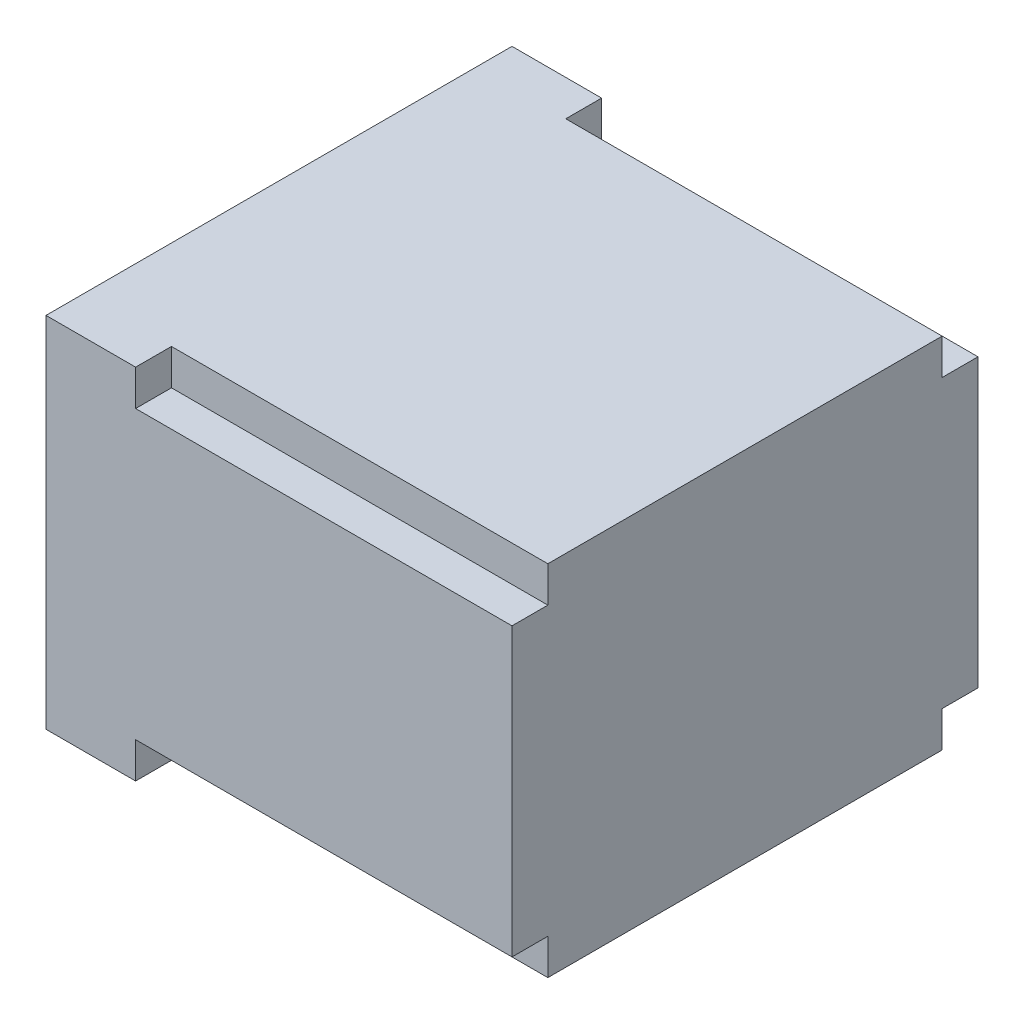
SolidWorks part; units mm, degrees
ref_plane "Front Plane" through (0, 0, 0) normal (0, 0, 1) x (1, 0, 0)
ref_plane "Top Plane" through (0, 0, 0) normal (0, 1, 0) x (1, 0, 0)
ref_plane "Right Plane" through (0, 0, 0) normal (1, 0, 0) x (0, 0, -1)
sketch "Sketch2" plane through (0, 0, 0) normal (0, 1, 0) x (1, 0, 0)
  line L1 (0, 0) -> (130, 0)
  line L2 (0, 0) -> (0, 130)
  line L3 (0, 130) -> (130, 130)
  line L4 (130, 0) -> (130, 130)
  dimension "D1" = 130
  dimension "D2" = 130
extrude "Boss-Extrude1" add sketch "Sketch2" along normal blind 100
sketch "Sketch3" plane through (0, 0, 0) normal (-1, 0, 0) x (0, 0, 1)
  line L0 (-130, 100) -> (0, 100) construction
  line L1 (-117, 13) -> (-13, 13)
  line L2 (-117, 13) -> (-117, 87)
  line L3 (-117, 87) -> (-13, 87)
  line L4 (-13, 13) -> (-13, 87)
  line L5 (0, 100) -> (0, 0) construction
  line L6 (-130, 0) -> (0, 0) construction
  line L7 (-130, 100) -> (-130, 0) construction
  dimension "D1" = 13
  dimension "D2" = 13
  dimension "D3" = 13
  dimension "D4" = 13
extrude "Cut-Extrude1" cut sketch "Sketch3" against normal blind 127
sketch "Sketch4" plane through (130, 0, 0) normal (1, 0, 0) x (0, 0, -1)
  line L1 (0, 100) -> (10, 100)
  line L2 (0, 100) -> (0, 90)
  line L3 (0, 90) -> (10, 90)
  line L4 (10, 100) -> (10, 90)
  line L5 (130, 100) -> (120, 100)
  line L6 (130, 100) -> (130, 90)
  line L7 (130, 90) -> (120, 90)
  line L8 (120, 100) -> (120, 90)
  line L9 (0, 0) -> (10, 0)
  line L10 (0, 0) -> (0, 10)
  line L11 (0, 10) -> (10, 10)
  line L12 (10, 0) -> (10, 10)
  line L13 (130, 0) -> (120, 0)
  line L14 (130, 0) -> (130, 10)
  line L15 (130, 10) -> (120, 10)
  line L16 (120, 0) -> (120, 10)
  dimension "D1" = 10
  dimension "D2" = 10
  dimension "D3" = 10
  dimension "D4" = 10
  dimension "D5" = 10
  dimension "D6" = 10
  dimension "D7" = 10
  dimension "D8" = 10
extrude "Cut-Extrude3" cut sketch "Sketch4" against normal blind 105
sketch "Sketch5" plane through (0, 0, 0) normal (-1, 0, 0) x (0, 0, 1)
  line L0 (-130, 100) -> (0, 100) construction
  line L1 (-117, 87) -> (-13, 87)
  line L2 (-117, 87) -> (-117, 97)
  line L3 (-117, 97) -> (-13, 97)
  line L4 (-13, 87) -> (-13, 97)
  line L5 (-117, 13) -> (-13, 13)
  line L6 (-117, 13) -> (-117, 3)
  line L7 (-117, 3) -> (-13, 3)
  line L8 (-13, 13) -> (-13, 3)
  line L9 (-130, 0) -> (0, 0) construction
  line L10 (0, 100) -> (0, 0) construction
  dimension "D1" = 3
  dimension "D2" = 3
  dimension "D3" = 13
  dimension "D4" = 13
extrude "Cut-Extrude4" cut sketch "Sketch5" against normal blind 127
sketch "Sketch6" plane through (0, 0, 0) normal (-1, 0, 0) x (0, 0, 1)
  line L0 (-117, 97) -> (-117, 3) construction
  line L1 (-117, 87) -> (-127, 87)
  line L2 (-117, 87) -> (-117, 13)
  line L3 (-117, 13) -> (-127, 13)
  line L4 (-127, 87) -> (-127, 13)
  line L5 (-13, 3) -> (-13, 97) construction
  line L6 (-13, 87) -> (-3, 87)
  line L7 (-13, 87) -> (-13, 13)
  line L8 (-13, 13) -> (-3, 13)
  line L9 (-3, 87) -> (-3, 13)
  line L10 (-130, 100) -> (-130, 0) construction
  line L11 (0, 100) -> (0, 0) construction
  line L12 (-130, 100) -> (0, 100) construction
  line L13 (-130, 0) -> (0, 0) construction
  dimension "D1" = 3
  dimension "D2" = 3
  dimension "D3" = 13
  dimension "D4" = 13
  dimension "D5" = 13
  dimension "D6" = 13
extrude "Cut-Extrude5" cut sketch "Sketch6" against normal blind 127
sketch "Sketch7" plane through (0, 0, 0) normal (-1, 0, 0) x (0, 0, 1)
  line L0 (0, 100) -> (0, 0) construction
  line L1 (-130, 0) -> (0, 0) construction
  line L2 (-130, 100) -> (-130, 0) construction
  line L3 (-130, 100) -> (0, 100) construction
  circle A0 centre (-124, 94) radius 1.75
  circle A1 centre (-6, 94) radius 1.75
  circle A2 centre (-124, 6) radius 1.75
  circle A3 centre (-6, 6) radius 1.75
  dimension "D3" = 3.5
  dimension "D6" = 3.5
  dimension "D9" = 3.5
  dimension "D12" = 3.5
  dimension "D1" = 6
  dimension "D2" = 6
  dimension "D4" = 6
  dimension "D5" = 6
  dimension "D7" = 6
  dimension "D8" = 6
  dimension "D10" = 6
  dimension "D11" = 6
extrude "Cut-Extrude6" cut sketch "Sketch7" against normal blind 20
sketch "Sketch8" plane through (0, 0, 0) normal (-1, 0, 0) x (0, 0, 1)
  line L1 (-117, 87) -> (-120, 87)
  line L2 (-117, 87) -> (-117, 90)
  line L3 (-117, 90) -> (-120, 90)
  line L4 (-120, 87) -> (-120, 90)
  line L5 (-13, 87) -> (-10, 87)
  line L6 (-13, 87) -> (-13, 90)
  line L7 (-13, 90) -> (-10, 90)
  line L8 (-10, 87) -> (-10, 90)
  line L9 (-117, 13) -> (-120, 13)
  line L10 (-117, 13) -> (-117, 10)
  line L11 (-117, 10) -> (-120, 10)
  line L12 (-120, 13) -> (-120, 10)
  line L13 (-13, 13) -> (-10, 13)
  line L14 (-13, 13) -> (-13, 10)
  line L15 (-13, 10) -> (-10, 10)
  line L16 (-10, 13) -> (-10, 10)
  dimension "D1" = 3
  dimension "D2" = 3
  dimension "D3" = 3
  dimension "D4" = 3
  dimension "D5" = 3
  dimension "D6" = 3
  dimension "D7" = 3
  dimension "D8" = 3
extrude "Cut-Extrude7" cut sketch "Sketch8" against normal blind 5
sketch "Sketch9" plane through (0, 3, 0) normal (0, 1, 0) x (1, 0, 0)
  line L1 (0, 117) -> (85, 117)
  line L2 (0, 117) -> (0, 57)
  line L3 (0, 57) -> (85, 57)
  line L4 (85, 117) -> (85, 57)
  dimension "D1" = 60
  dimension "D2" = 85
extrude "Boss-Extrude2" add sketch "Sketch9" along normal blind 15
sketch "Sketch11" plane through (0, 13, 0) normal (0, 1, 0) x (1, 0, 0)
  line L0 (0, 127) -> (0, 120) construction
  line L5 (85, 117) -> (0, 117)
  line L6 (85, 117) -> (85, 123)
  line L7 (85, 123) -> (0, 123)
  line L8 (0, 117) -> (0, 123)
  dimension "D1" = 6
extrude "Boss-Extrude5" add sketch "Sketch11" along normal blind 5
sketch "Sketch12" plane through (0, 18, 0) normal (0, 1, 0) x (1, 0, 0)
  line L0 (85, 57) -> (85, 123) construction
  line L1 (0, 123) -> (85, 123)
  line L2 (0, 123) -> (0, 120)
  line L3 (0, 120) -> (85, 120)
  line L4 (85, 123) -> (85, 120)
  dimension "D1" = 3
extrude "Cut-Extrude9" cut sketch "Sketch12" against normal blind 4
sketch "Sketch13" plane through (0, 18, 0) normal (0, 1, 0) x (1, 0, 0)
  line L0 (85, 57) -> (85, 120) construction
  line L1 (82, 117) -> (0, 117)
  line L2 (82, 117) -> (82, 60)
  line L3 (82, 60) -> (0, 60)
  line L4 (0, 117) -> (0, 60)
  line L5 (0, 57) -> (85, 57) construction
  line L6 (0, 120) -> (85, 120) construction
  line L7 (0, 120) -> (0, 57) construction
  dimension "D1" = 3
  dimension "D2" = 3
  dimension "D3" = 3
  dimension "D4" = 0
extrude "Cut-Extrude10" cut sketch "Sketch13" against normal blind 15
sketch "Sketch15" plane through (5, 0, 0) normal (-1, 0, 0) x (0, 0, 1)
  line L1 (-120, 13) -> (-117, 13)
  line L2 (-120, 13) -> (-120, 10)
  line L3 (-120, 10) -> (-117, 10)
  line L4 (-117, 13) -> (-117, 10)
extrude "Boss-Extrude7" add sketch "Sketch15" along normal blind 5
sketch "Sketch16" plane through (0, 0, -60) normal (0, 0, -1) x (-1, 0, 0)
  line L0 (0, 3) -> (0, 18) construction
  line L1 (-82, 18) -> (0, 18)
  line L2 (-82, 18) -> (-82, 16)
  line L3 (-82, 16) -> (0, 16)
  line L4 (0, 18) -> (0, 16)
  line L5 (-82, 3) -> (-82, 18) construction
  line L6 (-82, 13) -> (0, 13)
  line L7 (-82, 13) -> (-82, 11)
  line L8 (-82, 11) -> (0, 11)
  line L9 (0, 13) -> (0, 11)
  dimension "D1" = 2
  dimension "D2" = 2
  dimension "D3" = 3
extrude "Boss-Extrude8" add sketch "Sketch16" along normal blind 57
sketch "Sketch17" plane through (0, 18, 0) normal (0, 1, 0) x (1, 0, 0)
  line L0 (0, 120) -> (0, 57) construction
  line L1 (0, 112) -> (77, 112)
  line L2 (0, 112) -> (0, 65)
  line L3 (0, 65) -> (77, 65)
  line L4 (77, 112) -> (77, 65)
  line L5 (0, 57) -> (85, 57) construction
  line L6 (85, 57) -> (85, 120) construction
  line L7 (0, 120) -> (85, 120) construction
  dimension "D1" = 8
  dimension "D2" = 8
  dimension "D3" = 8
extrude "Cut-Extrude11" cut sketch "Sketch17" against normal blind 10
sketch "Sketch19" plane through (0, 0, -117) normal (0, 0, 1) x (1, 0, 0)
  line L1 (0, 11) -> (7, 11)
  line L2 (0, 11) -> (0, 9)
  line L3 (0, 9) -> (7, 9)
  line L4 (7, 11) -> (7, 9)
  line L5 (0, 13) -> (7, 13)
  line L6 (0, 13) -> (0, 14)
  line L7 (0, 14) -> (7, 14)
  line L8 (7, 13) -> (7, 14)
  dimension "D1" = 2
  dimension "D2" = 7
  dimension "D3" = 7
  dimension "D4" = 1
extrude "Boss-Extrude9" add sketch "Sketch19" along normal blind 1
sketch "Sketch21" plane through (0, 0, 0) normal (-1, 0, 0) x (0, 0, 1)
  line L0 (-130, 0) -> (0, 0) construction
  line L1 (-120, 13) -> (-117, 13)
  line L2 (-120, 13) -> (-120, 10)
  line L3 (-120, 10) -> (-117, 10)
  line L4 (-117, 13) -> (-117, 10)
  line L5 (-130, 100) -> (-130, 0) construction
  dimension "D1" = 3
  dimension "D2" = 3
  dimension "D3" = 10
  dimension "D4" = 10
extrude "Cut-Extrude15" cut sketch "Sketch21" against normal blind 5
